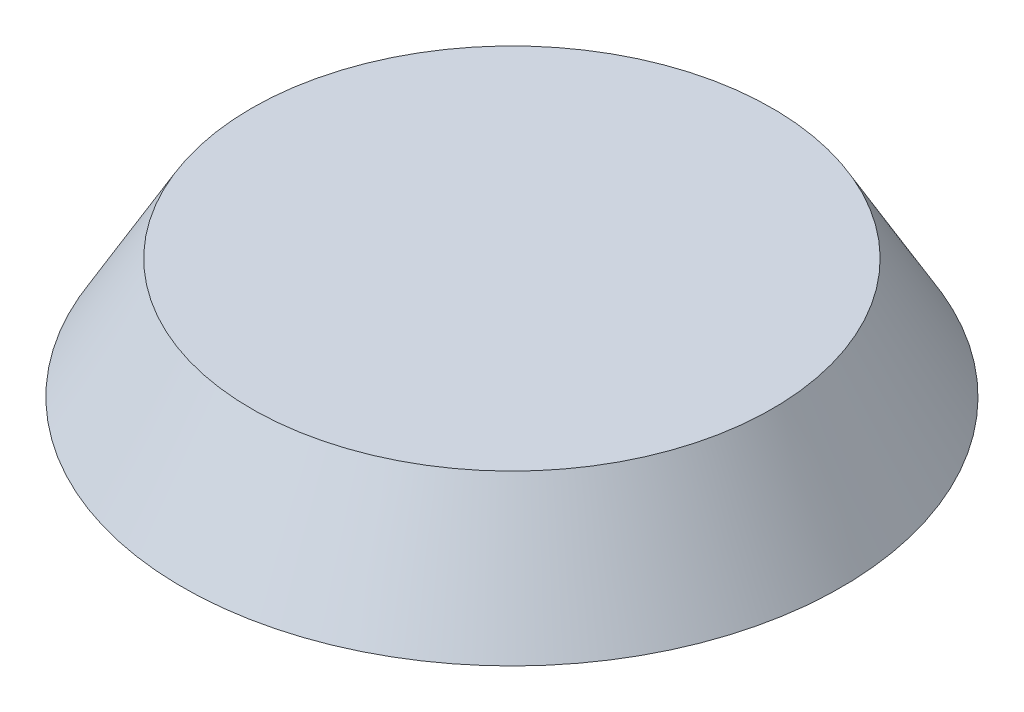
SolidWorks part; units mm, degrees
ref_plane "Front Plane" through (0, 0, 0) normal (0, 0, 1) x (1, 0, 0)
ref_plane "Top Plane" through (0, 0, 0) normal (0, 1, 0) x (1, 0, 0)
ref_plane "Right Plane" through (0, 0, 0) normal (1, 0, 0) x (0, 0, -1)
sketch "Sketch2" plane through (0, 0, 0) normal (0, 1, 0) x (1, 0, 0)
  line L9 (-4.2, 18.6) -> (-4.2, 22.6133)
  line L10 (4.2, 18.6) -> (4.2, 22.6133)
  line L11 (4.2, -18.6) -> (4.2, -22.6133)
  line L12 (-4.2, -18.6) -> (-4.2, -22.6133)
  line L13 (-18.6, 4.2) -> (-22.6133, 4.2)
  line L14 (-18.6, -4.2) -> (-22.6133, -4.2)
  line L15 (18.6, -4.2) -> (22.6133, -4.2)
  line L16 (18.6, 4.2) -> (22.6133, 4.2)
  circle A0 centre (0, 0) radius 23.15 construction
  arc A9 (-4.2, 22.6133) -> (-22.6133, 4.2) centre (0, 0) ccw
  arc A10 (22.6133, 4.2) -> (4.2, 22.6133) centre (0, 0) ccw
  arc A11 (-22.6133, -4.2) -> (-4.2, -22.6133) centre (0, 0) ccw
  arc A12 (4.2, -22.6133) -> (22.6133, -4.2) centre (0, 0) ccw
  arc A13 (-4.2, 18.6) -> (4.2, 18.6) centre (0, 18.6) ccw
  arc A14 (-4.2, -18.6) -> (4.2, -18.6) centre (0, -18.6) cw
  arc A15 (-18.6, -4.2) -> (-18.6, 4.2) centre (-18.6, 0) ccw
  arc A16 (18.6, -4.2) -> (18.6, 4.2) centre (18.6, 0) cw
  point P24 (0, 0)
  point P25 (0, 0)
  dimension "D1" = 46.3
extrude "Boss-Extrude1" add sketch "Sketch2" against normal blind 5 draft 1
sketch "Sketch4" plane through (0, 0, 0) normal (0, 0, 1) x (1, 0, 0)
  line L0 (0, 0) -> (55, 0)
  line L1 (55, 0) -> (43.453, 20)
  line L2 (43.453, 20) -> (0, 20)
  line L3 (0, 20) -> (0, 0)
  line L7 (24.8746, 0) -> (-24.8746, 0) construction
  dimension "D1" = 55
  dimension "D2" = 60
  dimension "D3" = 20
  dimension "D4" = 0
revolve "Revolve1" add sketch "Sketch4" angle 360 about L3
equation "\"D1@Sketch2\"=46.3"
